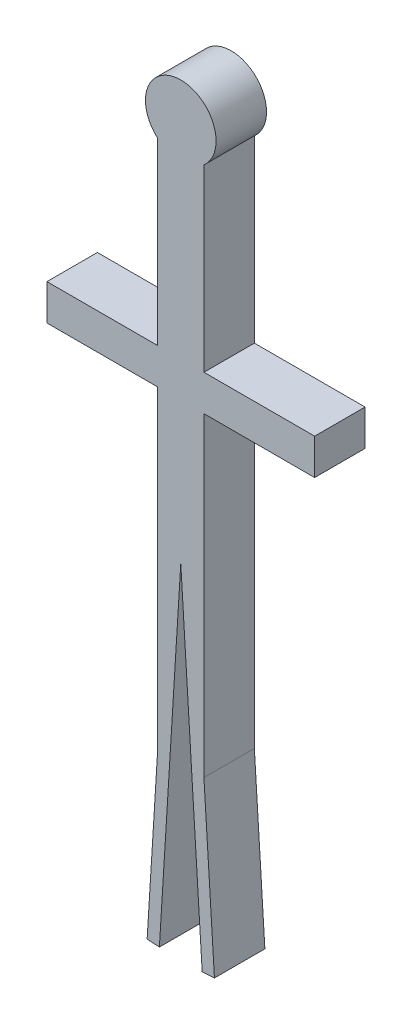
SolidWorks part; units mm, degrees
ref_plane "Front Plane" through (0, 0, 0) normal (0, 0, 1) x (1, 0, 0)
ref_plane "Top Plane" through (0, 0, 0) normal (0, 1, 0) x (1, 0, 0)
ref_plane "Right Plane" through (0, 0, 0) normal (1, 0, 0) x (0, 0, -1)
sketch "Sketch1" plane through (0, 0, 0) normal (0, 0, 1) x (1, 0, 0)
  line L0 (-58.2727, -67.138) -> (-58.2727, -519.3468)
  line L1 (-58.2727, -519.3468) -> (-336.9749, -519.3468)
  line L2 (-336.9749, -519.3468) -> (-336.9749, -609.622)
  line L3 (-336.9749, -609.622) -> (-58.2727, -609.622)
  line L4 (-58.2727, -609.622) -> (-58.2727, -1403.1187)
  line L5 (-58.2727, -1403.1187) -> (-84.7301, -1826.8745)
  line L6 (-84.7301, -1826.8745) -> (-53.8899, -1828.8)
  line L7 (-53.8899, -1828.8) -> (0, -965.671)
  line L8 (0, -965.671) -> (53.8899, -1828.8)
  line L9 (53.8899, -1828.8) -> (84.7301, -1826.8745)
  line L10 (84.7301, -1826.8745) -> (58.2727, -1403.1187)
  line L11 (58.2727, -1403.1187) -> (58.2727, -609.622)
  line L12 (58.2727, -609.622) -> (336.9749, -609.622)
  line L13 (336.9749, -609.622) -> (336.9749, -519.3468)
  line L14 (336.9749, -519.3468) -> (58.2727, -519.3468)
  line L15 (58.2727, -519.3468) -> (58.2727, -67.138)
  line L16 (0, 175.0846) -> (0, -1061.3734) construction
  line L18 (-131.6529, -449.1794) -> (165.4225, -449.1794) construction
  line L19 (-304.5575, -348.5817) -> (290.9285, -348.5817) construction
  arc A0 (58.2727, -67.138) -> (-58.2727, -67.138) centre (0, 0) ccw
  dimension "D1" = 177.8
  dimension "D2" = 1828.8
extrude "Boss-Extrude2" add sketch "Sketch1" along normal blind 127
